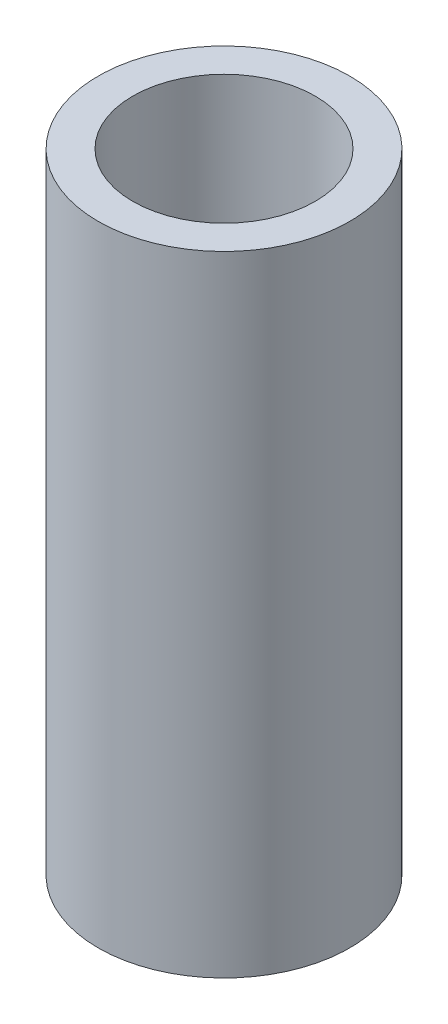
SolidWorks part; units mm, degrees
ref_plane "Front Plane" through (0, 0, 0) normal (0, 0, 1) x (1, 0, 0)
ref_plane "Top Plane" through (0, 0, 0) normal (0, 1, 0) x (1, 0, 0)
ref_plane "Right Plane" through (0, 0, 0) normal (1, 0, 0) x (0, 0, -1)
sketch "Sketch1" plane through (0, 0, 0) normal (0, 1, 0) x (1, 0, 0)
  circle A0 centre (0, 0) radius 2
  circle A1 centre (0, 0) radius 1.45
  dimension "D1" = 4
  dimension "D2" = 2.9
extrude "Boss-Extrude1" add sketch "Sketch1" along normal blind 10
